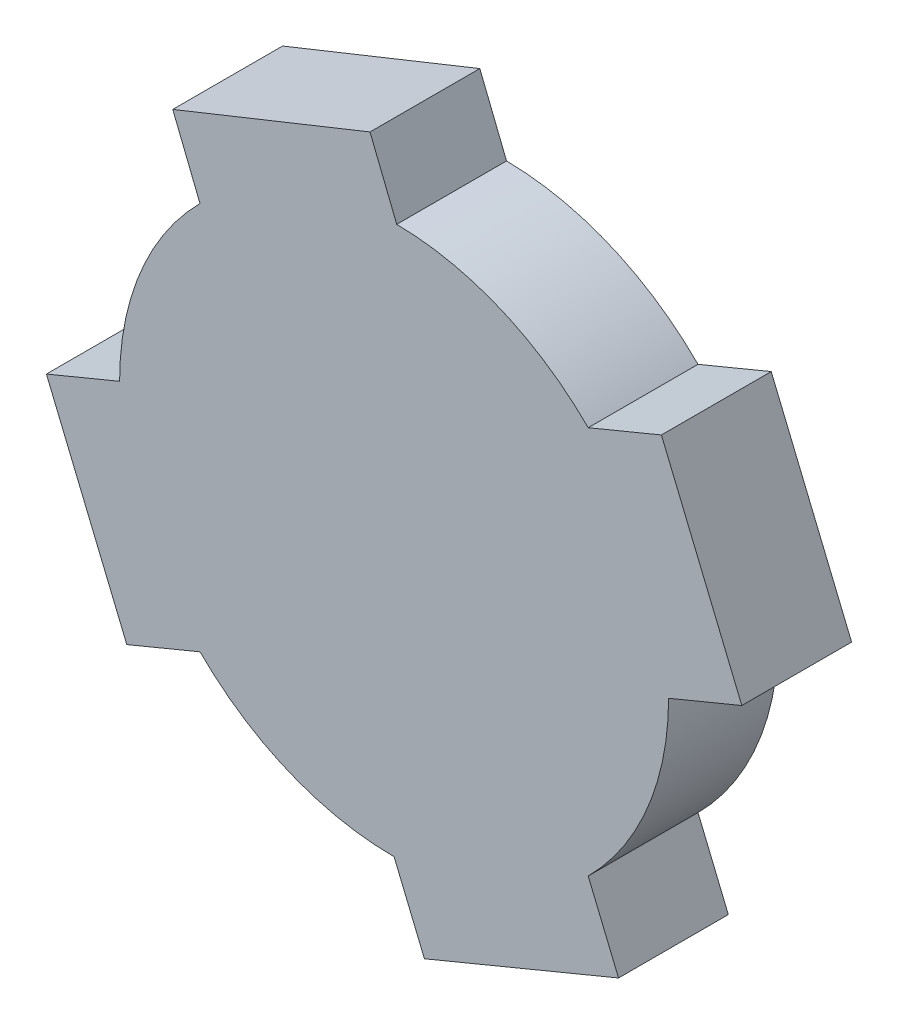
SolidWorks part; units mm, degrees
ref_plane "Front Plane" through (0, 0, 0) normal (0, 0, 1) x (1, 0, 0)
ref_plane "Top Plane" through (0, 0, 0) normal (0, 1, 0) x (1, 0, 0)
ref_plane "Right Plane" through (0, 0, 0) normal (1, 0, 0) x (0, 0, -1)
sketch "Sketch1" plane through (0, 0, 0) normal (0, 0, 1) x (1, 0, 0)
  circle A0 centre (0, 0) radius 75
  dimension "D1" = 150
extrude "Boss-Extrude1" add sketch "Sketch1" along normal blind 30
sketch "Sketch4" plane through (0, 0, 30) normal (0, 0, 1) x (1, 0, 0)
  line L0 (75, 0) -> (53.033, 53.033)
  line L1 (75, 0) -> (53.033, 53.033)
  line L2 (53.033, 53.033) -> (0, 75)
  line L3 (0, 75) -> (-53.033, 53.033)
  line L4 (-53.033, 53.033) -> (-75, 0)
  line L5 (-75, 0) -> (-53.033, -53.033)
  line L6 (-53.033, -53.033) -> (0, -75)
  line L7 (0, -75) -> (53.033, -53.033)
  line L8 (53.033, -53.033) -> (75, 0)
  line L9 (75, 0) -> (95, 8.2843)
  line L10 (53.033, 53.033) -> (73.033, 61.3173)
  line L11 (95, 8.2843) -> (73.033, 61.3173)
  line L12 (-53.033, -53.033) -> (-75, 0)
  line L13 (-53.033, -53.033) -> (-73.033, -61.3173)
  line L14 (-75, 0) -> (-95, -8.2843)
  line L15 (-73.033, -61.3173) -> (-95, -8.2843)
  line L16 (53.033, -53.033) -> (0, -75)
  line L17 (53.033, -53.033) -> (61.3173, -73.033)
  line L18 (0, -75) -> (8.2843, -95)
  line L19 (61.3173, -73.033) -> (8.2843, -95)
  line L20 (0.8615, 74.6432) -> (-53.033, 53.033)
  line L21 (0.8615, 74.6432) -> (-6.5819, 93.2065)
  line L22 (-53.033, 53.033) -> (-60.4764, 71.5963)
  line L23 (-6.5819, 93.2065) -> (-60.4764, 71.5963)
  circle A0 centre (0, 0) radius 69.291 construction
  circle M16 centre (0, 0) radius 75
  dimension "D1" = 20
  dimension "D2" = 20
  dimension "D3" = 20
  dimension "D4" = 20
extrude "Boss-Extrude2" add sketch "Sketch4" against normal up to surface (30 mm away) contours L19 L17 L18 M16 | L9 L11 L10 M16 | L15 L13 L14 M16 | L21 L23 L22 M16 up to face at (75, 0, 0)
